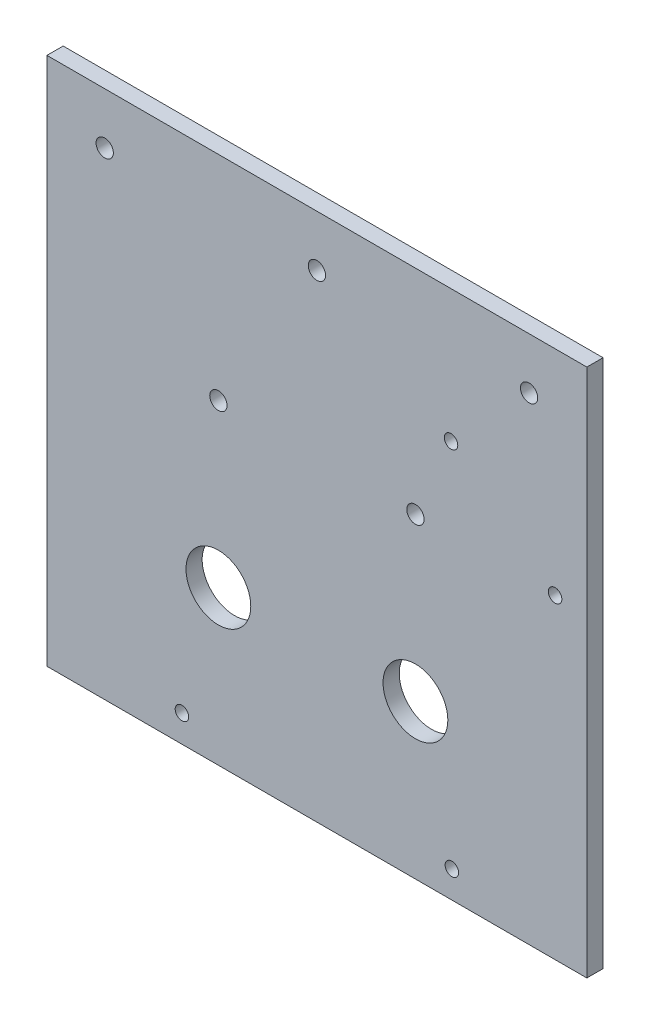
SolidWorks part; units mm, degrees
ref_plane "正面" through (0, 0, 0) normal (0, 0, 1) x (1, 0, 0)
ref_plane "平面" through (0, 0, 0) normal (0, 1, 0) x (1, 0, 0)
ref_plane "右側面" through (0, 0, 0) normal (1, 0, 0) x (0, 0, -1)
sketch "ｽｹｯﾁ1" plane through (0, 0, 0) normal (0, 0, 1) x (1, 0, 0)
  line L1 (-50, 49.5) -> (50, 49.5)
  line L2 (-50, 49.5) -> (-50, -49.5)
  line L3 (-50, -49.5) -> (50, -49.5)
  line L4 (50, 49.5) -> (50, -49.5)
  line L5 (-50, 49.5) -> (50, -49.5) construction
  line L6 (-50, -49.5) -> (50, 49.5) construction
  point P0 (0, 0)
  dimension "D1" = 100
  dimension "D2" = 99
extrude "ﾎﾞｽ - 押し出し1" add sketch "ｽｹｯﾁ1" along normal blind 3
sketch "ｽｹｯﾁ2" plane through (0, 0, 3) normal (0, 0, 1) x (1, 0, 0)
  line L0 (0, 0) -> (18.25, 0)
  line L1 (0, 0) -> (-18.25, 0)
  line L2 (-18.25, 0) -> (-18.25, -20)
  line L3 (18.25, 0) -> (18.25, -20)
  line L4 (0, 0) -> (0, 40)
  line L5 (-5.12, 9.7) -> (-2.4542, 19.649)
  line L6 (-18.25, -20) -> (-18.25, -43.5)
  line L7 (-18.25, -43.5) -> (-25, -43.5)
  line L8 (18.25, -20) -> (18.25, -43.5)
  line L9 (18.25, -43.5) -> (25, -43.5)
  line L10 (0, 40) -> (24.84, 40)
  line L11 (24.84, 40) -> (47.04, 40)
  line L12 (47.04, 40) -> (47.04, 29.7)
  line L13 (0, 40) -> (-27.32, 40)
  line L14 (-27.32, 40) -> (-27.32, 20)
  line L15 (-27.32, 20) -> (-5.12, 20)
  line L16 (-5.12, 20) -> (-5.12, 9.7)
  line L17 (-2.4542, 19.649) -> (-23.8977, 25.3948)
  circle A0 centre (18.25, 0) radius 1.6
  circle A1 centre (-18.25, 0) radius 1.6
  circle A2 centre (-18.25, -20) radius 6
  circle A3 centre (18.25, -20) radius 6
  circle A4 centre (0, 40) radius 1.6
  circle A5 centre (-25, -43.5) radius 1.5
  circle A6 centre (25, -43.5) radius 1.5
  circle A7 centre (24.84, 40) radius 1.5
  circle A8 centre (47.04, 29.7) radius 1.5
  circle A9 centre (-27.32, 20) radius 1.5
  circle A10 centre (-5.12, 9.7) radius 1.5
  circle A11 centre (-23.8977, 25.3948) radius 1.5
  dimension "D3" = 3.2
  dimension "D4" = 3.2
  dimension "D7" = 12
  dimension "D8" = 12
  dimension "D10" = 3.2
  dimension "D15" = 3
  dimension "D16" = 3
  dimension "D18" = 3
  dimension "D21" = 3
  dimension "D26" = 3
  dimension "D27" = 3
  dimension "D31" = 3
  dimension "D1" = 18.25
  dimension "D2" = 18.25
  dimension "D5" = 20
  dimension "D6" = 20
  dimension "D9" = 40
  dimension "D11" = 23.5
  dimension "D12" = 6.75
  dimension "D13" = 23.5
  dimension "D14" = 6.75
  dimension "D17" = 24.84
  dimension "D19" = 22.2
  dimension "D20" = 10.3
  dimension "D22" = 27.32
  dimension "D23" = 20
  dimension "D24" = 22.2
  dimension "D25" = 10.3
  dimension "D28" = 10.3
  dimension "D29" = 22.2
  dimension "D30" = 15
extrude "ｶｯﾄ - 押し出し1" cut sketch "ｽｹｯﾁ2" against normal blind 3 contours L10 A4 L13 | L13 A4 L4 | L4 A4 L10 | L6 A2 L2 | L2 A2 L6 | L3 A3 L8 | L8 A3 L3 | A0
sketch "ｽｹｯﾁ4" plane through (0, -49.5, 0) normal (0, -1, 0) x (-1, 0, 0)
  line L1 (-65.0352, 7.2729) -> (66.9264, 7.2729)
  line L2 (-65.0352, 7.2729) -> (-65.0352, -9.5375)
  line L3 (-65.0352, -9.5375) -> (66.9264, -9.5375)
  line L4 (66.9264, 7.2729) -> (66.9264, -9.5375)
  line L5 (-65.0352, 7.2729) -> (66.9264, -9.5375) construction
  line L6 (-65.0352, -9.5375) -> (66.9264, 7.2729) construction
  point P0 (0.9456, -1.1323)
extrude "ｶｯﾄ - 押し出し2" cut sketch "ｽｹｯﾁ4" against normal blind 1
sketch "ｽｹｯﾁ7" plane through (0, 0, 0) normal (0, 0, -1) x (-1, 0, 0)
  line L0 (-24.84, 40) -> (-24.84, 25)
  line L1 (-24.84, 25) -> (-47.04, 29.7)
  line L2 (-47.04, 29.7) -> (-47.04, 19.4)
  line L3 (-24.84, 25) -> (-44.1226, 9.9348)
  circle A0 centre (-24.84, 25) radius 1.7111
  circle A1 centre (-47.04, 19.4) radius 1.8009
  circle A2 centre (-44.1226, 9.9348) radius 1.6401
  dimension "D1" = 22.6921
  dimension "D2" = 10.3
  dimension "D3" = 15
  dimension "D4" = 24.47
  dimension "D5" = 128
hole_wizard "M3x0.5 ねじ穴4" positions "3Dｽｹｯﾁ4" profile "ｽｹｯﾁ9" tap size "M3x0.5" standard "JIS"
sketch3d "3Dｽｹｯﾁ4"
  point P0 (25, -43.5, 3)
  point P3 (-25, -43.5, 3)
sketch "ｽｹｯﾁ9" plane through (25, -43.5, 3) normal (1, 0, 0) x (0, -1, 0)
  line L0 (0, 0) -> (0, 9.2511)
  line L1 (0, 9.2511) -> (1.25, 8.5)
  line L2 (1.25, 8.5) -> (1.25, 0)
  line L5 (1.25, 0) -> (0, 0)
  line L10 (0, 9.2511) -> (-1.25, 8.5) construction
  line L11 (0, -6.35) -> (0, 107.95) construction
  dimension "ねじ下穴ﾄﾞﾘﾙ直径" = 2.5
  dimension "ねじ下穴ﾄﾞﾘﾙの深さ" = 8.5
  dimension "ﾄﾞﾘﾙ角度" = 118
cosmetic thread "穴のねじ山15" parameters "D1"=3, "D2"=3
cosmetic thread "穴のねじ山16" parameters "D1"=3, "D2"=3
hole_wizard "M3x0.5 ねじ穴5" positions "3Dｽｹｯﾁ5" profile "ｽｹｯﾁ10" tap size "M3x0.5" standard "JIS"
sketch3d "3Dｽｹｯﾁ5"
  point P0 (44.1226, 9.9348, 0)
  point P3 (24.84, 25, 0)
sketch "ｽｹｯﾁ10" plane through (44.1226, 9.9348, 0) normal (1, 0, 0) x (0, 1, 0)
  line L0 (0, 0) -> (0, 9.2511)
  line L1 (0, 9.2511) -> (1.25, 8.5)
  line L2 (1.25, 8.5) -> (1.25, 0)
  line L5 (1.25, 0) -> (0, 0)
  line L10 (0, 9.2511) -> (-1.25, 8.5) construction
  line L11 (0, -6.35) -> (0, 107.95) construction
  dimension "ねじ下穴ﾄﾞﾘﾙ直径" = 2.5
  dimension "ねじ下穴ﾄﾞﾘﾙの深さ" = 8.5
  dimension "ﾄﾞﾘﾙ角度" = 118
cosmetic thread "穴のねじ山11" parameters "D1"=3, "D2"=3
cosmetic thread "穴のねじ山12" parameters "D1"=3, "D2"=3
sketch "ｽｹｯﾁ11" plane through (0, 0, 0) normal (0, 0, -1) x (-1, 0, 0)
  line L0 (0, 0) -> (0, 10)
  line L1 (0, 0) -> (0, 40) construction
  line L2 (0, 10) -> (18.25, 10)
  line L3 (0, 10) -> (-18.25, 10)
  circle A0 centre (18.25, 10) radius 1.6
  circle A1 centre (-18.25, 10) radius 1.6
  dimension "D2" = 3.2
  dimension "D3" = 3.2
  dimension "D1" = 10
extrude "ｶｯﾄ - 押し出し3" cut sketch "ｽｹｯﾁ11" against normal blind 10
sketch "ｽｹｯﾁ12" plane through (0, 0, 0) normal (0, 0, -1) x (-1, 0, 0)
  line L0 (0, 40) -> (39.3, 40)
  line L1 (0, 40) -> (-39.3, 40)
  line L2 (-24.84, 40) -> (-47.04, 40) construction
  circle A0 centre (-39.3, 40) radius 1.6
  circle A1 centre (39.3, 40) radius 1.6
  dimension "D3" = 3.2
  dimension "D4" = 3.2
  dimension "D1" = 39.3
  dimension "D2" = 39.3
extrude "ｶｯﾄ - 押し出し4" cut sketch "ｽｹｯﾁ12" against normal blind 10
